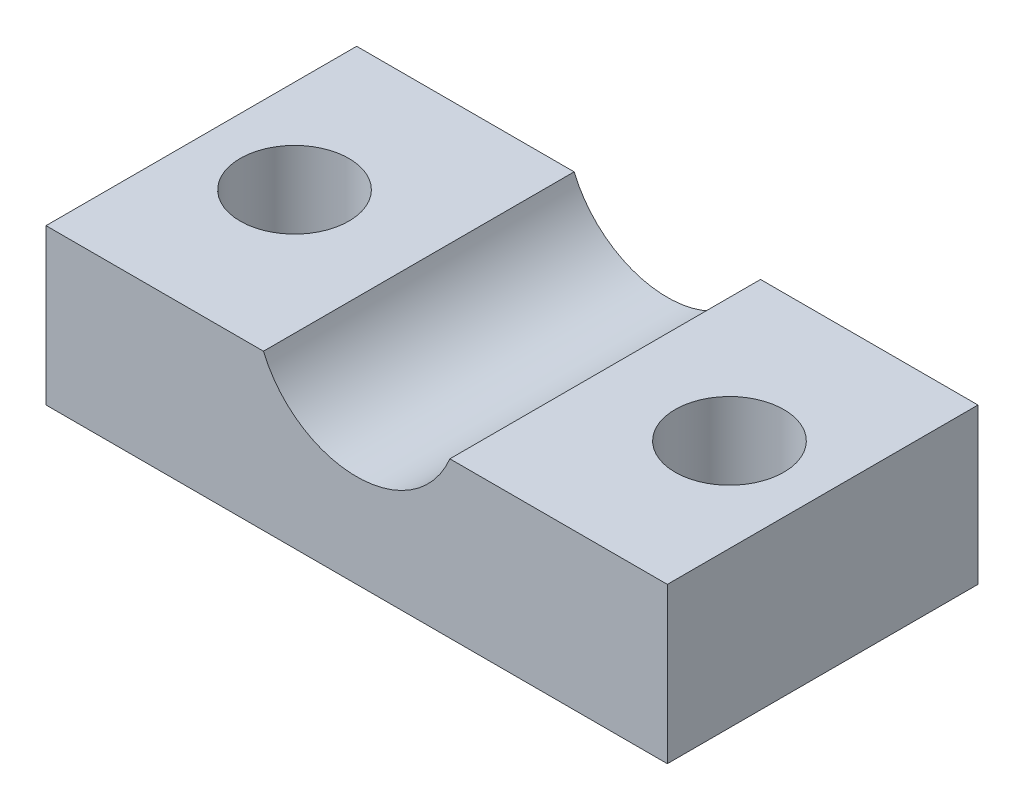
SolidWorks part; units mm, degrees
ref_plane "Ebene vorne" through (0, 0, 0) normal (0, 0, 1) x (1, 0, 0)
ref_plane "Ebene oben" through (0, 0, 0) normal (0, 1, 0) x (1, 0, 0)
ref_plane "Ebene rechts" through (0, 0, 0) normal (1, 0, 0) x (0, 0, -1)
sketch "Skizze1" plane through (0, 0, 0) normal (0, 0, 1) x (1, 0, 0)
  line L0 (0, 0) -> (20, 0)
  line L1 (20, 0) -> (20, 5)
  line L2 (20, 5) -> (13, 5)
  line L3 (0, 0) -> (0, 5)
  line L4 (0, 5) -> (7, 5)
  arc A0 (7, 5) -> (13, 5) centre (10, 6.25) ccw
  point P7 (10, 3)
  dimension "D1" = 7
  dimension "D2" = 7
  dimension "D3" = 2
  dimension "D4" = 5
  dimension "D5" = 20
  dimension "D6" = 0
  dimension "D7" = 0
  dimension "D8" = 0
extrude "Aufsatz-Linear austragen1" add sketch "Skizze1" along normal blind 10
sketch "Skizze2" plane through (0, 5, 0) normal (0, 1, 0) x (1, 0, 0)
  line L0 (7, 0) -> (0, 0) construction
  line L1 (0, -10) -> (0, 0) construction
  line L2 (20, -10) -> (20, 0) construction
  circle A0 centre (3, -5) radius 1.75
  circle A1 centre (17, -5) radius 1.75
  point P8 (3.6796, -4.9104)
  dimension "D5" = 3.5
  dimension "D6" = 3.5
  dimension "D1" = 5
  dimension "D2" = 0
  dimension "D3" = 3
  dimension "D4" = 3
extrude "Schnitt-Linear austragen1" cut sketch "Skizze2" against normal through all
